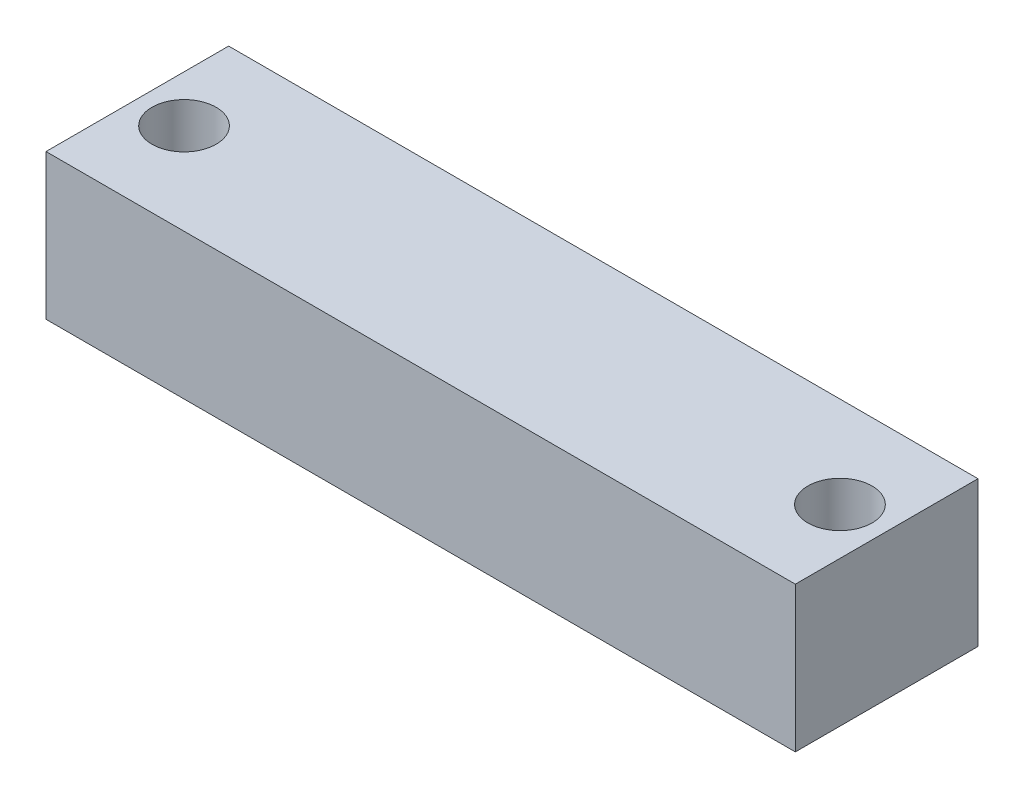
SolidWorks part; units mm, degrees
ref_plane "Front Plane" through (0, 0, 0) normal (0, 0, 1) x (1, 0, 0)
ref_plane "Top Plane" through (0, 0, 0) normal (0, 1, 0) x (1, 0, 0)
ref_plane "Right Plane" through (0, 0, 0) normal (1, 0, 0) x (0, 0, -1)
sketch "Sketch1" plane through (0, 0, 0) normal (0, 1, 0) x (1, 0, 0)
  line L1 (-45.125, -11) -> (45.125, -11)
  line L2 (-45.125, -11) -> (-45.125, 11)
  line L3 (-45.125, 11) -> (45.125, 11)
  line L4 (45.125, -11) -> (45.125, 11)
  line L5 (-45.125, -11) -> (45.125, 11) construction
  line L6 (-45.125, 11) -> (45.125, -11) construction
  point P0 (0, 0)
  dimension "D1" = 90.25
  dimension "D2" = 22
extrude "Boss-Extrude1" add sketch "Sketch1" along normal blind 17.5
sketch "Sketch2" plane through (0, 17.5, 0) normal (0, 1, 0) x (1, 0, 0)
  line L0 (0, 11) -> (0, -11) construction
  line L1 (45.125, 11) -> (-45.125, 11) construction
  line L2 (-45.125, -11) -> (45.125, -11) construction
  line L3 (-45.125, 0) -> (45.125, 0) construction
  line L4 (-45.125, 11) -> (-45.125, -11) construction
  line L5 (45.125, -11) -> (45.125, 11) construction
  circle A0 centre (-39.5, 0) radius 1.5
  circle A1 centre (39.5, 0) radius 1.5
  dimension "D2" = 3
  dimension "D1" = 79
extrude "Cut-Extrude1" cut sketch "Sketch2" against normal through all and the other way through all
sketch "Sketch3" plane through (0, 17.5, 0) normal (0, 1, 0) x (1, 0, 0)
  line L1 (-43.365, 11) -> (-43.365, -11)
  line L2 (-45.125, 11) -> (-45.125, -11) construction
  line L3 (45.125, 11) -> (-45.125, 11) construction
  line L4 (-45.125, -11) -> (45.125, -11) construction
  circle A0 centre (-39.5, 0) radius 3.865
  circle A1 centre (39.5, 0) radius 3.865
  circle M2 centre (-39.5, 0) radius 1.5
  circle M3 centre (39.5, 0) radius 1.5
  dimension "D1" = 1.76
extrude "Cut-Extrude2" cut sketch "Sketch3" against normal blind 10 contours A0 M2 | A1 M3
